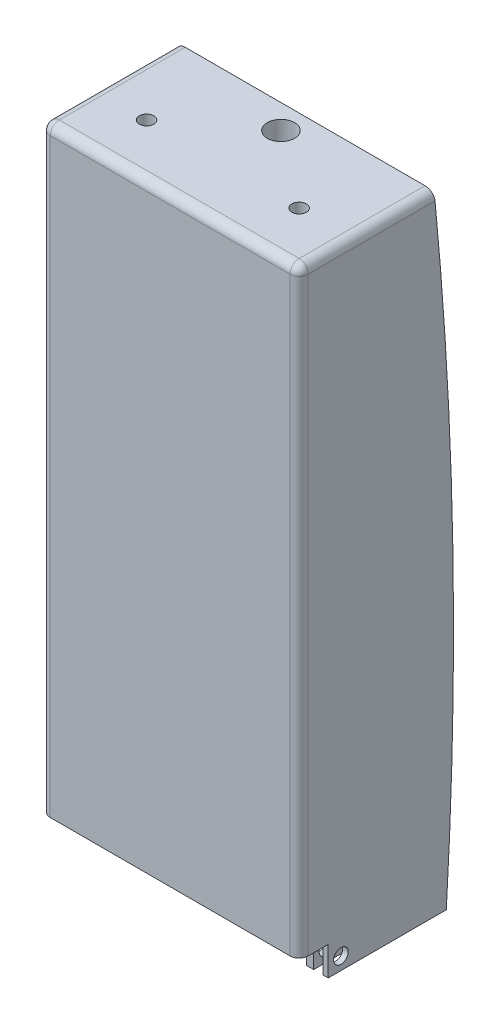
SolidWorks part; units mm, degrees
ref_plane "Front Plane" through (0, 0, 0) normal (0, 0, 1) x (1, 0, 0)
ref_plane "Top Plane" through (0, 0, 0) normal (0, 1, 0) x (1, 0, 0)
ref_plane "Right Plane" through (0, 0, 0) normal (1, 0, 0) x (0, 0, -1)
sketch "Sketch4" plane through (0, 0, 0) normal (0, 0, 1) x (1, 0, 0)
  line L0 (-65, 350) -> (-65, 10)
  line L1 (-55, 0) -> (55, 0)
  line L2 (65, 10) -> (65, 350)
  line L3 (65, 350) -> (-65, 350)
  line L4 (0, 0) -> (0, 180.0439) construction
  arc A0 (-55, 0) -> (-65, 10) centre (-55, 10) cw
  arc A1 (55, 0) -> (65, 10) centre (55, 10) ccw
  point P6 (-65, 0)
  dimension "D3" = 10
  dimension "D4" = 10
  dimension "D1" = 130
  dimension "D2" = 350
  dimension "D5" = 0
  dimension "D6" = 65
sketch "Sketch6" plane through (0, 0, 0) normal (1, 0, 0) x (0, 0, -1)
  line L0 (0, 10) -> (0, 350) construction
  line L1 (45, 356) -> (-45, 356)
  line L2 (45, 356) -> (45, 344)
  line L3 (45, 344) -> (-45, 344)
  line L4 (-45, 356) -> (-45, 344)
  line L5 (45, 356) -> (-45, 344) construction
  line L6 (45, 344) -> (-45, 356) construction
  point P0 (0, 350)
  dimension "D1" = 90
  dimension "D2" = 12
sweep "Sweep2" add profiles "Sketch6" path "Sketch4"
sketch "Sketch7" plane through (0, 0, 0) normal (0, 1, 0) x (1, 0, 0)
  line L1 (-80.8354, -49.7013) -> (80.8354, -49.7013)
  line L2 (-80.8354, -49.7013) -> (-80.8354, 49.7013)
  line L3 (-80.8354, 49.7013) -> (80.8354, 49.7013)
  line L4 (80.8354, -49.7013) -> (80.8354, 49.7013)
  line L5 (-80.8354, -49.7013) -> (80.8354, 49.7013) construction
  line L6 (-80.8354, 49.7013) -> (80.8354, -49.7013) construction
  point P0 (0, 0)
extrude "Cut-Extrude1" cut sketch "Sketch7" against normal blind 10 and the other way blind 10
sketch "Sketch8" plane through (0, 0, 0) normal (0, 1, 0) x (1, 0, 0)
  line L0 (0, -45) -> (0, 45) construction
  line L1 (-68, -46.7578) -> (-63, -46.7578)
  line L2 (-68, -46.7578) -> (-68, 47.2422)
  line L3 (-68, 47.2422) -> (-63, 47.2422)
  line L4 (-63, -46.7578) -> (-63, 47.2422)
  line L5 (-68, -46.7578) -> (-63, 47.2422) construction
  line L6 (-68, 47.2422) -> (-63, -46.7578) construction
  line L7 (68, 47.2422) -> (63, 47.2422)
  line L8 (63, -46.7578) -> (63, 47.2422)
  line L9 (68, -46.7578) -> (63, -46.7578)
  line L10 (68, -46.7578) -> (68, 47.2422)
  point P0 (-65.5, 0.2422)
  dimension "D1" = 5
  dimension "D2" = 63
  dimension "D3" = 94
extrude "Cut-Extrude2" cut sketch "Sketch8" along normal blind 35
sketch "Sketch9" plane through (0, 356, 0) normal (0, 1, 0) x (1, 0, 0)
  line L0 (0, 0) -> (-71, 0) construction
  line L1 (-71, -45) -> (-71, 45) construction
  line L2 (0, 45) -> (0, -45) construction
  circle A0 centre (0, 0) radius 7.5
  circle A1 centre (-42, 32) radius 4
  circle A2 centre (-42, -32) radius 4
  circle A3 centre (42, -32) radius 4
  circle A4 centre (42, 32) radius 4
  dimension "D1" = 15
  dimension "D2" = 8
  dimension "D3" = 8
  dimension "D4" = 32
  dimension "D5" = 32
  dimension "D6" = 42
  dimension "D7" = 42
extrude "Cut-Extrude3" cut sketch "Sketch9" against normal through all
sketch "Sketch10" plane through (71, 0, 0) normal (1, 0, 0) x (0, 0, -1)
  line L0 (45, 10) -> (-45, 10) construction
  line L1 (-45, 356) -> (-45, 10) construction
  circle A0 centre (-38, 17) radius 4
  dimension "D1" = 8
  dimension "D2" = 7
  dimension "D3" = 7
extrude "Cut-Extrude4" cut sketch "Sketch10" against normal through all
sketch "Sketch11" plane through (0, 356, 0) normal (0, 1, 0) x (1, 0, 0)
  line L1 (-71, -61) -> (71, -61)
  line L2 (-71, -61) -> (-71, -45)
  line L3 (-71, -45) -> (71, -45)
  line L4 (71, -61) -> (71, -45)
  line L5 (-71, -61) -> (71, -45) construction
  line L6 (-71, -45) -> (71, -61) construction
  point P0 (0, -53)
  dimension "D1" = 142
  dimension "D2" = 16
extrude "Boss-Extrude1" add sketch "Sketch11" against normal blind 330
fillet "Fillet2" radius 5 3 edges at (63, 22.5, -45) (61, 10, -45) (59, 177, -45)
fillet "Fillet3" radius 5 3 edges at (68, 22.5, -45) (71, 183, -45) (69.5, 10, -45)
fillet "Fillet4" radius 5 3 edges at (-61, 10, -45) (-59, 177, -45) (-63, 22.5, -45)
fillet "Fillet5" radius 5 3 edges at (-69.5, 10, -45) (-68, 22.5, -45) (-71, 183, -45)
fillet "Fillet6" radius 5 9 edges at (71, 356, 10.5) (69.5355, 356, -43.5355) (33, 356, -45) (-33, 356, -45) (-69.5355, 356, -43.5355) (-71, 356, 10.5) (0, 356, 61) (-71, 191, 61) (71, 191, 61)
sketch "Sketch12" plane through (-71, 0, 0) normal (-1, 0, 0) x (0, 0, 1)
  line L0 (-19.9981, 10) -> (-79.773, 10)
  line L1 (-40, 10) -> (45, 10) construction
  line L2 (-79.773, 10) -> (-79.773, 406.4421)
  line L3 (-79.773, 406.4421) -> (-12.8836, 360.2403)
  arc A0 (-19.9981, 10) -> (-12.8836, 360.2403) centre (2146.0324, 141.1932) cw
  dimension "D1" = 2170
  dimension "D2" = 59.7749
extrude "Cut-Extrude5" cut sketch "Sketch12" against normal through all
